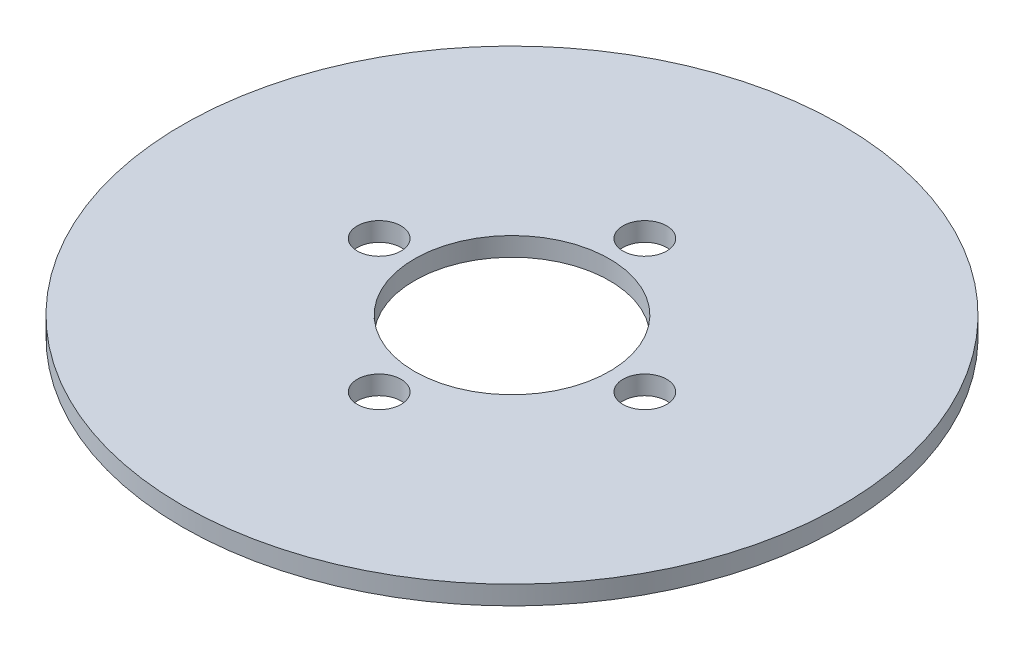
SolidWorks part; units mm, degrees
material "1060 Alloy"
ref_plane "Front Plane" through (0, 0, 0) normal (0, 0, 1) x (1, 0, 0)
ref_plane "Top Plane" through (0, 0, 0) normal (0, 1, 0) x (1, 0, 0)
ref_plane "Right Plane" through (0, 0, 0) normal (1, 0, 0) x (0, 0, -1)
sketch "Sketch1" plane through (0, 0, 0) normal (0, 1, 0) x (1, 0, 0)
  circle A0 centre (0, 0) radius 49
  circle A1 centre (0, 0) radius 14.5
  circle A2 centre (0, 19.75) radius 3.25
  circle A3 centre (19.75, 0) radius 3.25
  circle A4 centre (0, -19.75) radius 3.25
  circle A5 centre (-19.75, 0) radius 3.25
  point P6 (0, 14.5)
  point P7 (0, 0)
  point P10 (0, 16.5)
  point P17 (0, 0)
  dimension "D1" = 98
  dimension "D2" = 29
  dimension "D3" = 6.5
  dimension "D4" = 2
  dimension "D5" = 4
extrude "Boss-Extrude1" add sketch "Sketch1" along normal mid plane 2.8
